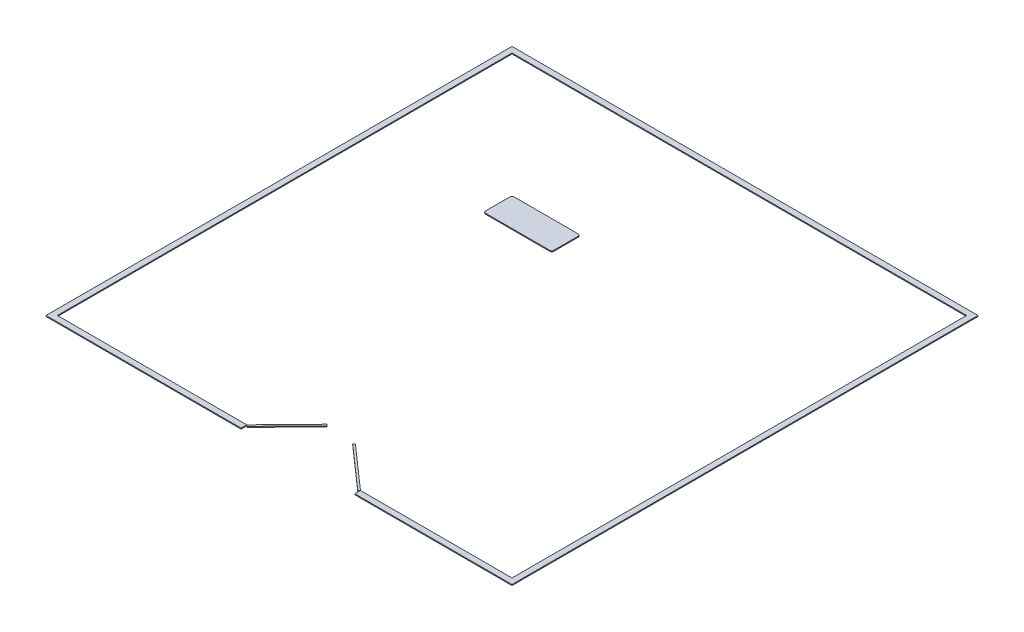
SolidWorks part; units mm, degrees
ref_plane "Front Plane" through (0, 0, 0) normal (0, 0, 1) x (1, 0, 0)
ref_plane "Top Plane" through (0, 0, 0) normal (0, 1, 0) x (1, 0, 0)
ref_plane "Right Plane" through (0, 0, 0) normal (1, 0, 0) x (0, 0, -1)
sketch "Sketch1" plane through (0, 0, 0) normal (0, 1, 0) x (1, 0, 0)
  line L0 (-152.4, 12344.4) -> (12344.4, 12344.4)
  line L1 (0, 0) -> (12192, 0)
  line L2 (0, 0) -> (0, 12192)
  line L3 (0, 12192) -> (12192, 12192)
  line L4 (12192, 0) -> (12192, 12192)
  line L5 (0, 0) -> (12192, 12192) construction
  line L6 (0, 12192) -> (12192, 0) construction
  line L7 (12344.4, -152.4) -> (12344.4, 12344.4)
  line L8 (-152.4, -152.4) -> (12344.4, -152.4)
  line L9 (-152.4, -152.4) -> (-152.4, 12344.4)
  point P4 (6096, 6096)
  dimension "D1" = 12192
  dimension "D2" = 152.4
extrude "Outside_Perim" add sketch "Sketch1" along normal blind 25.4
sketch "Sketch2" plane through (0, 25.4, 0) normal (0, 1, 0) x (1, 0, 0)
  line L0 (5080, 0) -> (5080, -152.4)
  line L1 (0, 0) -> (12192, 0) construction
  line L2 (-152.4, -152.4) -> (12344.4, -152.4) construction
  line L3 (8128, 0) -> (8128, -152.4)
  line L4 (0, 12192) -> (0, 0) construction
  line L5 (5080, 0) -> (8128, 0)
  line L6 (8128, -152.4) -> (5080, -152.4)
  dimension "D1" = 3048
  dimension "D2" = 5080
extrude "Doorway" cut sketch "Sketch2" against normal through all
sketch "Sketch3" plane through (0, 0, 0) normal (0, 1, 0) x (1, 0, 0)
  line L1 (3365.0551, 8877.6595) -> (5092.2551, 8877.6595)
  line L2 (3314.2551, 8826.8595) -> (3314.2551, 8166.4595)
  line L3 (3365.0551, 8115.6595) -> (5092.2551, 8115.6595)
  line L4 (5143.0551, 8826.8595) -> (5143.0551, 8166.4595)
  arc A0 (5092.2551, 8115.6595) -> (5143.0551, 8166.4595) centre (5092.2551, 8166.4595) ccw
  arc A1 (5092.2551, 8877.6595) -> (5143.0551, 8826.8595) centre (5092.2551, 8826.8595) cw
  arc A2 (3314.2551, 8166.4595) -> (3365.0551, 8115.6595) centre (3365.0551, 8166.4595) ccw
  arc A3 (3365.0551, 8877.6595) -> (3314.2551, 8826.8595) centre (3365.0551, 8826.8595) ccw
  point P8 (5143.0551, 8877.6595)
  point P11 (3314.2551, 8115.6595)
  point P14 (3314.2551, 8877.6595)
  dimension "D3" = 50.8
  dimension "D1" = 762
  dimension "D2" = 1828.8
extrude "Table" add sketch "Sketch3" along normal blind 25.4 separate body
sketch "Sketch4" plane through (0, 0, 0) normal (0, 1, 0) x (1, 0, 0)
  line L0 (5080, 0) -> (6143.3566, 1091.7183)
  line L1 (6143.3566, 1091.7183) -> (6179.7472, 1056.273)
  line L2 (6179.7472, 1056.273) -> (5116.3906, -35.4452)
  line L3 (5116.3906, -35.4452) -> (5080, 0)
  line L4 (8128, 0) -> (6984.8571, 1007.8692)
  line L5 (6984.8571, 1007.8692) -> (6951.2615, 969.7644)
  line L6 (6951.2615, 969.7644) -> (8091.3879, -35.4452)
  line L7 (8091.3879, -35.4452) -> (8128, 0)
  dimension "D1" = 1524
  dimension "D2" = 50.8
  dimension "D3" = 1524
  dimension "D4" = 50.8
extrude "Doors" add sketch "Sketch4" along normal blind 25.4 separate body
sketch "Sketch5" plane through (0, 0, 0) normal (0, 1, 0) x (1, 0, 0)
  line L0 (5080, 0) -> (6604, 0)
  line L1 (5080, 0) -> (4318, 1319.8227)
  line L2 (8128, 0) -> (6604, 0)
  line L3 (8128, 0) -> (8890, 1319.8227)
  arc A0 (6604, 0) -> (4318, 1319.8227) centre (5080, 0) ccw
  arc A1 (8890, 1319.8227) -> (6604, 0) centre (8128, 0) ccw
  dimension "D1" = 120
  dimension "D2" = 120
sketch "Sketch7" plane through (0, 0, 0) normal (0, 1, 0) x (1, 0, 0)
  line L0 (11004.4867, 1921.1506) -> (10286.3179, 1215.2233) construction
